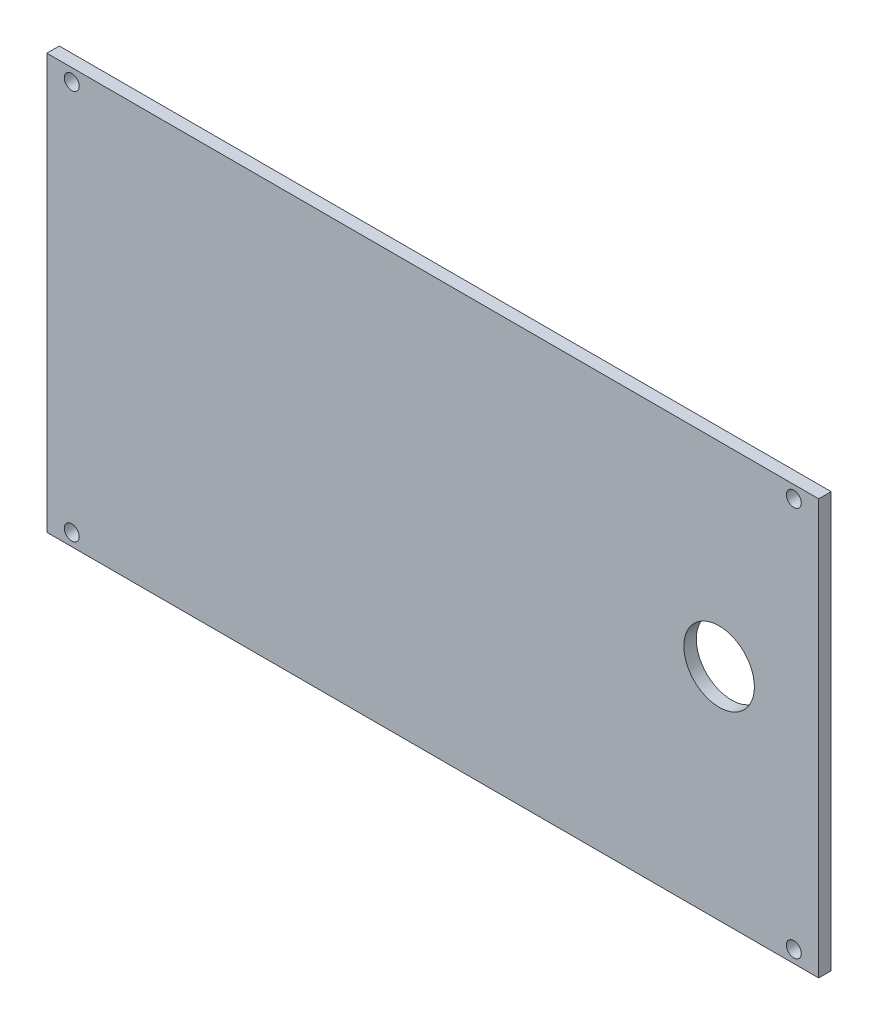
SolidWorks part; units mm, degrees
material "PMMA laser cult panels"
ref_plane "Front Plane" through (0, 0, 0) normal (0, 0, 1) x (1, 0, 0)
ref_plane "Top Plane" through (0, 0, 0) normal (0, 1, 0) x (1, 0, 0)
ref_plane "Right Plane" through (0, 0, 0) normal (1, 0, 0) x (0, 0, -1)
sketch "Sketch1" plane through (0, 0, 0) normal (0, 0, 1) x (1, 0, 0)
  line L1 (0, 0) -> (186, 0)
  line L2 (0, 0) -> (0, 100)
  line L3 (0, 100) -> (186, 100)
  line L4 (186, 0) -> (186, 100)
  dimension "D1" = 186
  dimension "D2" = 100
extrude "Boss-Extrude1" add sketch "Sketch1" along normal blind 3
sketch "Sketch2" plane through (0, 0, 3) normal (0, 0, 1) x (1, 0, 0)
  line L0 (0, 0) -> (186, 0) construction
  line L1 (180, 3) -> (6, 3)
  line L2 (180, 3) -> (180, 97)
  line L3 (180, 97) -> (6, 97)
  line L4 (6, 3) -> (6, 97)
  line L5 (186, 100) -> (0, 100) construction
  line L6 (186, 0) -> (186, 100) construction
  line L7 (0, 100) -> (0, 0) construction
  circle A0 centre (180, 3) radius 1.8
  circle A1 centre (180, 97) radius 1.8
  circle A2 centre (6, 97) radius 1.8
  circle A3 centre (6, 3) radius 1.8
  circle A4 centre (162, 53) radius 8.5
  dimension "D5" = 3.6
  dimension "D6" = 17
  dimension "D8" = 53
  dimension "D1" = 3
  dimension "D2" = 3
  dimension "D3" = 6
  dimension "D4" = 6
  dimension "D7" = 24
extrude "Cut-Extrude1" cut sketch "Sketch2" against normal through all contours A4 | A0 | A1 | A3 | A2
